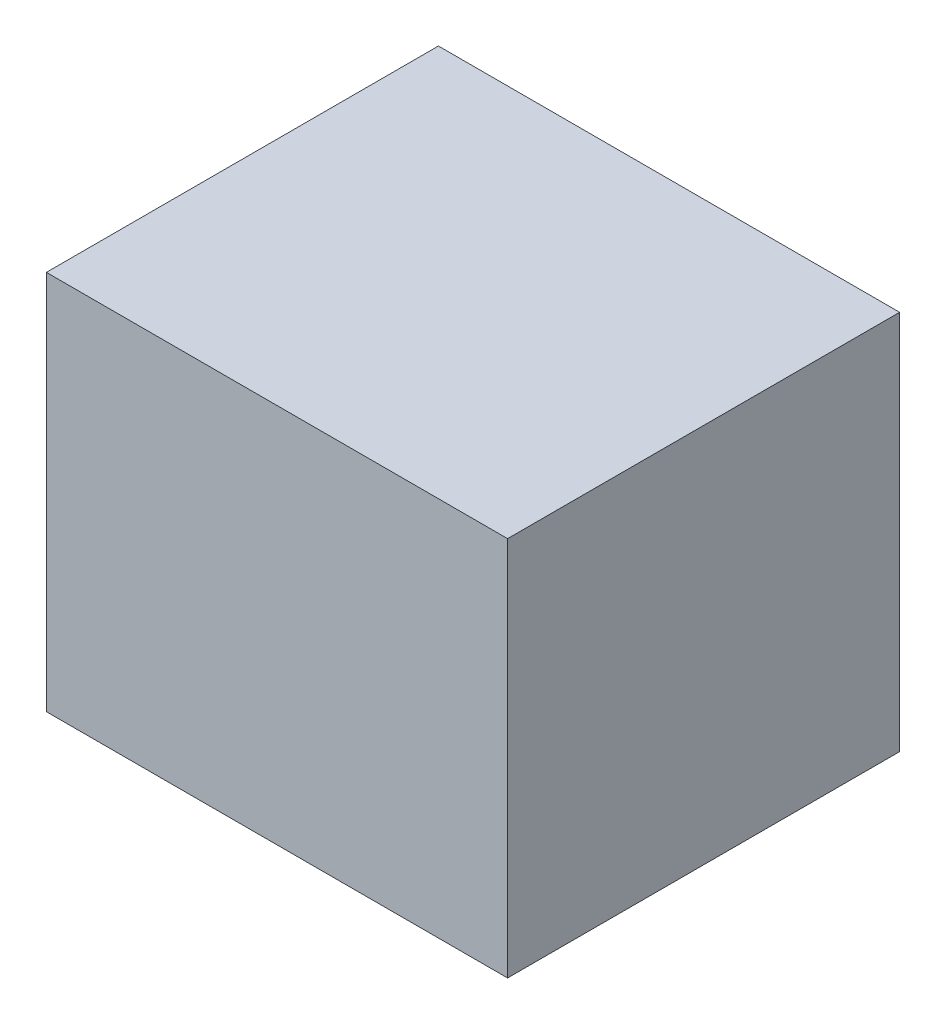
SolidWorks part; units mm, degrees
ref_plane "前基準面" through (0, 0, 0) normal (0, 0, 1) x (1, 0, 0)
ref_plane "上基準面" through (0, 0, 0) normal (0, 1, 0) x (1, 0, 0)
ref_plane "右基準面" through (0, 0, 0) normal (1, 0, 0) x (0, 0, -1)
sketch "草圖1" plane through (0, 0, 0) normal (0, 0, 1) x (1, 0, 0)
  line L1 (-86.9004, 60.2198) -> (113.0996, 60.2198)
  line L2 (-86.9004, 60.2198) -> (-86.9004, -104.7802)
  line L3 (-86.9004, -104.7802) -> (113.0996, -104.7802)
  line L4 (113.0996, 60.2198) -> (113.0996, -104.7802)
  dimension "D1" = 200
  dimension "D2" = 165
extrude "填料-伸長1" add sketch "草圖1" along normal blind 170
